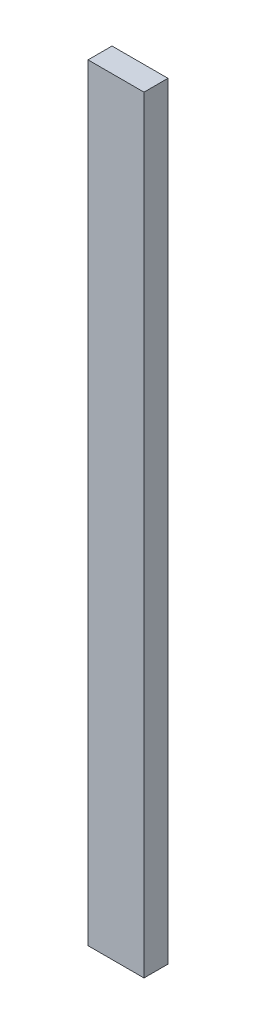
SolidWorks part; units mm, degrees
ref_plane "Front Plane" through (0, 0, 0) normal (0, 0, 1) x (1, 0, 0)
ref_plane "Top Plane" through (0, 0, 0) normal (0, 1, 0) x (1, 0, 0)
ref_plane "Right Plane" through (0, 0, 0) normal (1, 0, 0) x (0, 0, -1)
sketch "Sketch2" plane through (0, 0, 0) normal (0, 0, 1) x (1, 0, 0)
  line L0 (0, 0) -> (88.9, 0)
  line L1 (0, 0) -> (0, 1219.2)
  line L2 (88.9, 0) -> (88.9, 1219.2)
  line L4 (88.9, 1219.2) -> (0, 1219.2)
  point P0 (44.45, 0)
  dimension "D1" = 88.9
  dimension "D2" = 1219.2
  dimension "D4" = 90
extrude "Boss-Extrude1" add sketch "Sketch2" along normal blind 38.1
